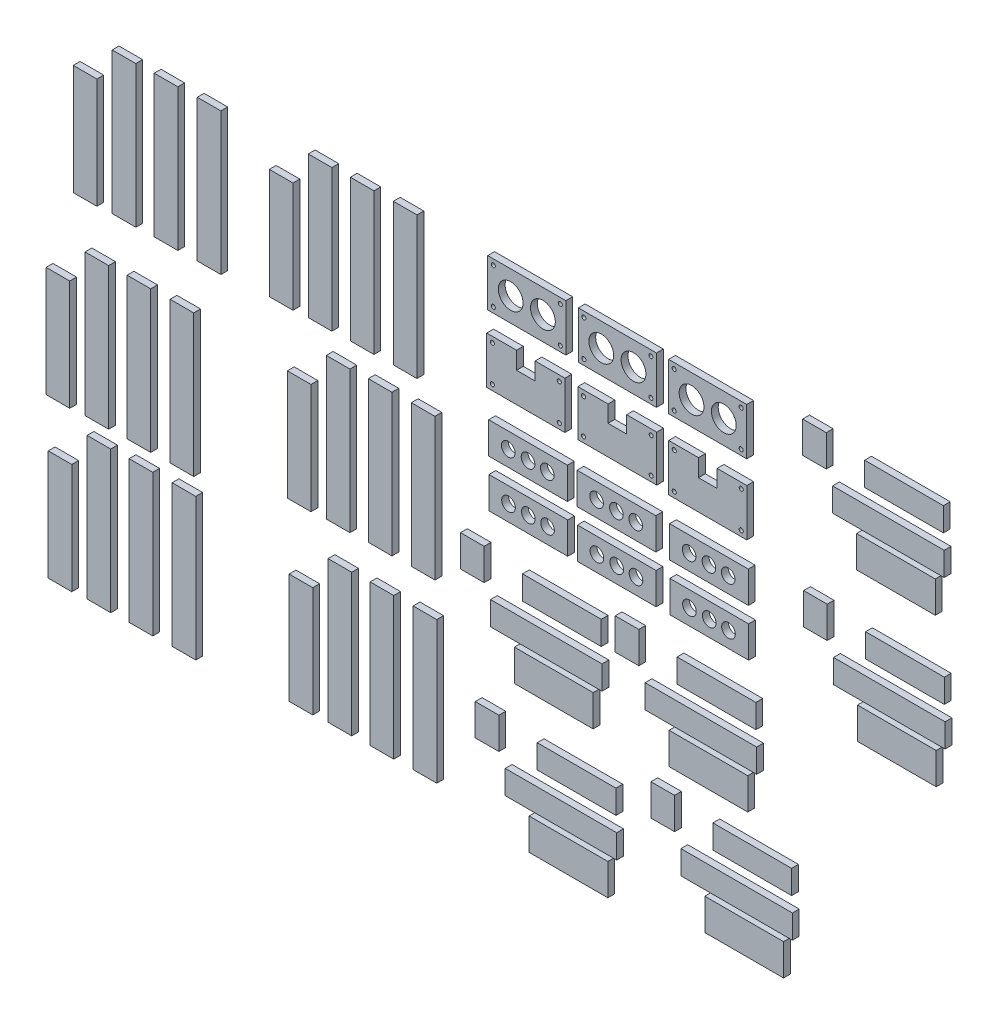
SolidWorks part; units mm, degrees
ref_plane "Alzado" through (0, 0, 0) normal (0, 0, 1) x (1, 0, 0)
ref_plane "Planta" through (0, 0, 0) normal (0, 1, 0) x (1, 0, 0)
ref_plane "Vista lateral" through (0, 0, 0) normal (1, 0, 0) x (0, 0, -1)
sketch "Croquis1" plane through (0, 0, 0) normal (0, 0, 1) x (1, 0, 0)
  line L0 (-40.6079, 0) -> (40.6079, 0) construction
  line L1 (-31.5, -19) -> (31.5, -19)
  line L2 (-31.5, -19) -> (-31.5, 19)
  line L3 (-31.5, 19) -> (31.5, 19)
  line L4 (31.5, -19) -> (31.5, 19)
  line L5 (-31.5, -19) -> (31.5, 19) construction
  line L6 (-31.5, 19) -> (31.5, -19) construction
  line L7 (0, 0) -> (0, -34.457) construction
  line L8 (-228.2882, -0.4654) -> (82.663, -0.4654) construction
  line L9 (-104.3126, -19.4654) -> (-41.3126, -19.4654)
  line L10 (-104.3126, -19.4654) -> (-104.3126, 18.5346)
  line L11 (-104.3126, 18.5346) -> (-41.3126, 18.5346)
  line L12 (-41.3126, -19.4654) -> (-41.3126, 18.5346)
  line L13 (-104.3126, -19.4654) -> (-41.3126, 18.5346) construction
  line L14 (-104.3126, 18.5346) -> (-41.3126, -19.4654) construction
  line L15 (-72.8126, -0.4654) -> (-72.8126, -34.9225) construction
  line L16 (-186.475, -0.4654) -> (-105.2592, -0.4654) construction
  line L17 (-177.3671, -19.4654) -> (-114.3671, -19.4654)
  line L18 (-177.3671, -19.4654) -> (-177.3671, 18.5346)
  line L19 (-177.3671, 18.5346) -> (-114.3671, 18.5346)
  line L20 (-114.3671, -19.4654) -> (-114.3671, 18.5346)
  line L21 (-177.3671, -19.4654) -> (-114.3671, 18.5346) construction
  line L22 (-177.3671, 18.5346) -> (-114.3671, -19.4654) construction
  line L23 (-145.8671, -0.4654) -> (-145.8671, -34.9225) construction
  line L24 (-146.6682, -54.9649) -> (-115.1682, -54.9649) construction
  line L25 (-178.1682, -73.9649) -> (-162.1682, -73.9649)
  line L26 (-178.1682, -73.9649) -> (-178.1682, -35.9649)
  line L27 (-178.1682, -35.9649) -> (-154.1682, -35.9649)
  line L28 (-115.1682, -73.9649) -> (-115.1682, -35.9649)
  line L29 (-178.1682, -73.9649) -> (-115.1682, -35.9649) construction
  line L30 (-178.1682, -35.9649) -> (-115.1682, -73.9649) construction
  line L31 (-146.6682, -54.9649) -> (-146.6682, -32.3728) construction
  line L32 (-131.1682, -73.9649) -> (-115.1682, -73.9649)
  line L33 (-139.1682, -35.9649) -> (-115.1682, -35.9649)
  line L34 (-154.1682, -35.9649) -> (-154.1682, -49.9649)
  line L35 (-154.1682, -49.9649) -> (-139.1682, -49.9649)
  line L36 (-139.1682, -35.9649) -> (-139.1682, -49.9649)
  line L37 (-162.1682, -73.9649) -> (-131.1682, -73.9649)
  line L38 (-72.8577, -55.1129) -> (-41.0716, -55.1129) construction
  line L39 (-104.6438, -73.6337) -> (-88.6438, -73.6337)
  line L40 (-104.6438, -73.6337) -> (-104.6438, -36.5921)
  line L41 (-104.6438, -36.5921) -> (-80.3577, -36.5921)
  line L42 (-41.0716, -73.6337) -> (-41.0716, -36.5921)
  line L43 (-104.6438, -73.6337) -> (-41.0716, -36.5921) construction
  line L44 (-104.6438, -36.5921) -> (-41.0716, -73.6337) construction
  line L45 (-72.8577, -55.1129) -> (-72.8577, -35.0223) construction
  line L46 (-57.6438, -73.6337) -> (-41.0716, -73.6337)
  line L47 (-65.3577, -36.5921) -> (-41.0716, -36.5921)
  line L48 (-80.3577, -36.5921) -> (-80.3577, -50.1129)
  line L49 (-80.3577, -50.1129) -> (-65.3577, -50.1129)
  line L50 (-65.3577, -36.5921) -> (-65.3577, -50.1129)
  line L51 (-88.6438, -73.6337) -> (-57.6438, -73.6337)
  line L52 (0.0494, -56.6209) -> (31.5494, -56.6209) construction
  line L53 (-31.4506, -75.6209) -> (-15.4506, -75.6209)
  line L54 (-31.4506, -75.6209) -> (-31.4506, -37.6209)
  line L55 (-31.4506, -37.6209) -> (-7.4506, -37.6209)
  line L56 (31.5494, -75.6209) -> (31.5494, -37.6209)
  line L57 (-31.4506, -75.6209) -> (31.5494, -37.6209) construction
  line L58 (-31.4506, -37.6209) -> (31.5494, -75.6209) construction
  line L59 (0.0494, -56.6209) -> (0.0494, -34.0287) construction
  line L60 (15.5494, -75.6209) -> (31.5494, -75.6209)
  line L61 (7.5494, -37.6209) -> (31.5494, -37.6209)
  line L62 (-7.4506, -37.6209) -> (-7.4506, -51.6209)
  line L63 (-7.4506, -51.6209) -> (7.5494, -51.6209)
  line L64 (7.5494, -37.6209) -> (7.5494, -51.6209)
  line L65 (-15.4506, -75.6209) -> (15.5494, -75.6209)
  line L66 (-288.1863, 17.873) -> (-269.1363, 17.873)
  line L67 (-253.4877, 18.4091) -> (-234.4377, 18.4091)
  line L68 (-253.4877, 18.4091) -> (-253.4877, -95.8909)
  line L69 (-253.4877, -95.8909) -> (-234.4377, -95.8909)
  line L70 (-234.4377, 18.4091) -> (-234.4377, -95.8909)
  line L71 (-288.1863, 17.873) -> (-288.1863, -96.427)
  line L72 (-288.1863, -96.427) -> (-269.1363, -96.427)
  line L73 (-269.1363, 17.873) -> (-269.1363, -96.427)
  line L74 (-322.0812, 17.1595) -> (-303.0312, 17.1595)
  line L75 (-322.0812, 17.1595) -> (-322.0812, -97.1405)
  line L76 (-322.0812, -97.1405) -> (-303.0312, -97.1405)
  line L77 (-303.0312, 17.1595) -> (-303.0312, -97.1405)
  line L78 (-353.4785, -9.3109) -> (-334.4285, -9.3109)
  line L79 (-353.4785, -9.3109) -> (-353.4785, -98.2109)
  line L80 (-353.4785, -98.2109) -> (-334.4285, -98.2109)
  line L81 (-334.4285, -9.3109) -> (-334.4285, -98.2109)
  line L82 (-50.4155, -216.2662) -> (39.5005, -216.2662)
  line L83 (-176.6177, -95.7144) -> (-113.1177, -95.7144)
  line L84 (-176.6177, -95.7144) -> (-176.6177, -121.1144)
  line L85 (-176.6177, -121.1144) -> (-113.1177, -121.1144)
  line L86 (-113.1177, -95.7144) -> (-113.1177, -121.1144)
  line L87 (-24.6254, -185.409) -> (38.8746, -185.409)
  line L88 (-24.6254, -185.409) -> (-24.6254, -204.459)
  line L89 (-24.6254, -204.459) -> (38.8746, -204.459)
  line L90 (38.8746, -185.409) -> (38.8746, -204.459)
  line L91 (-50.4155, -216.2662) -> (-50.4155, -235.3162)
  line L92 (-50.4155, -235.3162) -> (39.5005, -235.3162)
  line L93 (39.5005, -216.2662) -> (39.5005, -235.3162)
  line L94 (-105.3305, -95.344) -> (-41.8305, -95.344)
  line L95 (-105.3305, -95.344) -> (-105.3305, -120.744)
  line L96 (-31.1653, -239.8645) -> (32.3347, -239.8645)
  line L97 (-31.1653, -239.8645) -> (-31.1653, -265.2645)
  line L98 (-31.1653, -265.2645) -> (32.3347, -265.2645)
  line L99 (32.3347, -239.8645) -> (32.3347, -265.2645)
  line L100 (-74.5859, -181.6414) -> (-55.5359, -181.6414)
  line L101 (-74.5859, -181.6414) -> (-74.5859, -207.0414)
  line L102 (-74.5859, -207.0414) -> (-55.5359, -207.0414)
  line L103 (-55.5359, -181.6414) -> (-55.5359, -207.0414)
  line L104 (-105.3305, -120.744) -> (-41.8305, -120.744)
  line L105 (-41.8305, -95.344) -> (-41.8305, -120.744)
  line L106 (-30.7362, -95.344) -> (32.7638, -95.344)
  line L107 (-30.7362, -95.344) -> (-30.7362, -120.744)
  line L108 (-30.7362, -120.744) -> (32.7638, -120.744)
  line L109 (32.7638, -95.344) -> (32.7638, -120.744)
  line L110 (-176.3794, -133.8534) -> (-112.8794, -133.8534)
  line L111 (-176.3794, -133.8534) -> (-176.3794, -159.2534)
  line L112 (-176.3794, -159.2534) -> (-112.8794, -159.2534)
  line L113 (-112.8794, -133.8534) -> (-112.8794, -159.2534)
  line L114 (-105.0922, -133.4831) -> (-41.5922, -133.4831)
  line L115 (-105.0922, -133.4831) -> (-105.0922, -158.8831)
  line L116 (-105.0922, -158.8831) -> (-41.5922, -158.8831)
  line L117 (-41.5922, -133.4831) -> (-41.5922, -158.8831)
  line L118 (-30.4979, -133.4831) -> (33.0021, -133.4831)
  line L119 (-30.4979, -133.4831) -> (-30.4979, -158.8831)
  line L120 (-30.4979, -158.8831) -> (33.0021, -158.8831)
  line L121 (33.0021, -133.4831) -> (33.0021, -158.8831)
  line L122 (-446.3063, 11.4324) -> (-427.2563, 11.4324)
  line L123 (-411.6077, 11.9685) -> (-392.5577, 11.9685)
  line L124 (-411.6077, 11.9685) -> (-411.6077, -102.3315)
  line L125 (-411.6077, -102.3315) -> (-392.5577, -102.3315)
  line L126 (-392.5577, 11.9685) -> (-392.5577, -102.3315)
  line L127 (-446.3063, 11.4324) -> (-446.3063, -102.8676)
  line L128 (-446.3063, -102.8676) -> (-427.2563, -102.8676)
  line L129 (-427.2563, 11.4324) -> (-427.2563, -102.8676)
  line L130 (-480.2011, 10.7188) -> (-461.1511, 10.7188)
  line L131 (-480.2011, 10.7188) -> (-480.2011, -103.5812)
  line L132 (-480.2011, -103.5812) -> (-461.1511, -103.5812)
  line L133 (-461.1511, 10.7188) -> (-461.1511, -103.5812)
  line L134 (-511.5985, -15.7515) -> (-492.5485, -15.7515)
  line L135 (-511.5985, -15.7515) -> (-511.5985, -104.6515)
  line L136 (-511.5985, -104.6515) -> (-492.5485, -104.6515)
  line L137 (-492.5485, -15.7515) -> (-492.5485, -104.6515)
  line L138 (-468.2004, -140.5758) -> (-449.1504, -140.5758)
  line L139 (-433.5018, -140.0397) -> (-414.4518, -140.0397)
  line L140 (-433.5018, -140.0397) -> (-433.5018, -254.3397)
  line L141 (-433.5018, -254.3397) -> (-414.4518, -254.3397)
  line L142 (-414.4518, -140.0397) -> (-414.4518, -254.3397)
  line L143 (-468.2004, -140.5758) -> (-468.2004, -254.8758)
  line L144 (-468.2004, -254.8758) -> (-449.1504, -254.8758)
  line L145 (-449.1504, -140.5758) -> (-449.1504, -254.8758)
  line L146 (-502.0953, -141.2894) -> (-483.0453, -141.2894)
  line L147 (-502.0953, -141.2894) -> (-502.0953, -255.5894)
  line L148 (-502.0953, -255.5894) -> (-483.0453, -255.5894)
  line L149 (-483.0453, -141.2894) -> (-483.0453, -255.5894)
  line L150 (-533.4927, -167.7597) -> (-514.4427, -167.7597)
  line L151 (-533.4927, -167.7597) -> (-533.4927, -256.6597)
  line L152 (-533.4927, -256.6597) -> (-514.4427, -256.6597)
  line L153 (-514.4427, -167.7597) -> (-514.4427, -256.6597)
  line L154 (-273.655, -115.5539) -> (-254.605, -115.5539)
  line L155 (-238.9564, -115.0178) -> (-219.9064, -115.0178)
  line L156 (-238.9564, -115.0178) -> (-238.9564, -229.3178)
  line L157 (-238.9564, -229.3178) -> (-219.9064, -229.3178)
  line L158 (-219.9064, -115.0178) -> (-219.9064, -229.3178)
  line L159 (-273.655, -115.5539) -> (-273.655, -229.8539)
  line L160 (-273.655, -229.8539) -> (-254.605, -229.8539)
  line L161 (-254.605, -115.5539) -> (-254.605, -229.8539)
  line L162 (-307.5498, -116.2674) -> (-288.4998, -116.2674)
  line L163 (-307.5498, -116.2674) -> (-307.5498, -230.5674)
  line L164 (-307.5498, -230.5674) -> (-288.4998, -230.5674)
  line L165 (-288.4998, -116.2674) -> (-288.4998, -230.5674)
  line L166 (-338.9472, -142.7378) -> (-319.8972, -142.7378)
  line L167 (-338.9472, -142.7378) -> (-338.9472, -231.6378)
  line L168 (-338.9472, -231.6378) -> (-319.8972, -231.6378)
  line L169 (-319.8972, -142.7378) -> (-319.8972, -231.6378)
  line L170 (-466.5342, -267.8778) -> (-447.4842, -267.8778)
  line L171 (-431.8356, -267.3418) -> (-412.7856, -267.3418)
  line L172 (-431.8356, -267.3418) -> (-431.8356, -381.6418)
  line L173 (-431.8356, -381.6418) -> (-412.7856, -381.6418)
  line L174 (-412.7856, -267.3418) -> (-412.7856, -381.6418)
  line L175 (-466.5342, -267.8778) -> (-466.5342, -382.1778)
  line L176 (-466.5342, -382.1778) -> (-447.4842, -382.1778)
  line L177 (-447.4842, -267.8778) -> (-447.4842, -382.1778)
  line L178 (-500.429, -268.5914) -> (-481.379, -268.5914)
  line L179 (-500.429, -268.5914) -> (-500.429, -382.8914)
  line L180 (-500.429, -382.8914) -> (-481.379, -382.8914)
  line L181 (-481.379, -268.5914) -> (-481.379, -382.8914)
  line L182 (-531.8264, -295.0618) -> (-512.7764, -295.0618)
  line L183 (-531.8264, -295.0618) -> (-531.8264, -383.9618)
  line L184 (-531.8264, -383.9618) -> (-512.7764, -383.9618)
  line L185 (-512.7764, -295.0618) -> (-512.7764, -383.9618)
  line L186 (-272.2125, -256.7525) -> (-253.1625, -256.7525)
  line L187 (-237.5139, -256.2165) -> (-218.4639, -256.2165)
  line L188 (-237.5139, -256.2165) -> (-237.5139, -370.5165)
  line L189 (-237.5139, -370.5165) -> (-218.4639, -370.5165)
  line L190 (-218.4639, -256.2165) -> (-218.4639, -370.5165)
  line L191 (-272.2125, -256.7525) -> (-272.2125, -371.0525)
  line L192 (-272.2125, -371.0525) -> (-253.1625, -371.0525)
  line L193 (-253.1625, -256.7525) -> (-253.1625, -371.0525)
  line L194 (-306.1073, -257.4661) -> (-287.0573, -257.4661)
  line L195 (-306.1073, -257.4661) -> (-306.1073, -371.7661)
  line L196 (-306.1073, -371.7661) -> (-287.0573, -371.7661)
  line L197 (-287.0573, -257.4661) -> (-287.0573, -371.7661)
  line L198 (-337.5047, -283.9365) -> (-318.4547, -283.9365)
  line L199 (-337.5047, -283.9365) -> (-337.5047, -372.8365)
  line L200 (-337.5047, -372.8365) -> (-318.4547, -372.8365)
  line L201 (-318.4547, -283.9365) -> (-318.4547, -372.8365)
  line L202 (-175.1285, -220.5625) -> (-85.2125, -220.5625)
  line L203 (-149.3385, -189.7054) -> (-85.8385, -189.7054)
  line L204 (-149.3385, -189.7054) -> (-149.3385, -208.7554)
  line L205 (-149.3385, -208.7554) -> (-85.8385, -208.7554)
  line L206 (-85.8385, -189.7054) -> (-85.8385, -208.7554)
  line L207 (-175.1285, -220.5625) -> (-175.1285, -239.6125)
  line L208 (-175.1285, -239.6125) -> (-85.2125, -239.6125)
  line L209 (-85.2125, -220.5625) -> (-85.2125, -239.6125)
  line L210 (-155.8784, -244.1608) -> (-92.3784, -244.1608)
  line L211 (-155.8784, -244.1608) -> (-155.8784, -269.5608)
  line L212 (-155.8784, -269.5608) -> (-92.3784, -269.5608)
  line L213 (-92.3784, -244.1608) -> (-92.3784, -269.5608)
  line L214 (-199.299, -185.9377) -> (-180.249, -185.9377)
  line L215 (-199.299, -185.9377) -> (-199.299, -211.3377)
  line L216 (-199.299, -211.3377) -> (-180.249, -211.3377)
  line L217 (-180.249, -185.9377) -> (-180.249, -211.3377)
  line L218 (-163.2615, -332.5571) -> (-73.3455, -332.5571)
  line L219 (-137.4715, -301.6999) -> (-73.9715, -301.6999)
  line L220 (-137.4715, -301.6999) -> (-137.4715, -320.7499)
  line L221 (-137.4715, -320.7499) -> (-73.9715, -320.7499)
  line L222 (-73.9715, -301.6999) -> (-73.9715, -320.7499)
  line L223 (-163.2615, -332.5571) -> (-163.2615, -351.6071)
  line L224 (-163.2615, -351.6071) -> (-73.3455, -351.6071)
  line L225 (-73.3455, -332.5571) -> (-73.3455, -351.6071)
  line L226 (-144.0114, -356.1553) -> (-80.5114, -356.1553)
  line L227 (-144.0114, -356.1553) -> (-144.0114, -381.5553)
  line L228 (-144.0114, -381.5553) -> (-80.5114, -381.5553)
  line L229 (-80.5114, -356.1553) -> (-80.5114, -381.5553)
  line L230 (-187.432, -297.9322) -> (-168.382, -297.9322)
  line L231 (-187.432, -297.9322) -> (-187.432, -323.3322)
  line L232 (-187.432, -323.3322) -> (-168.382, -323.3322)
  line L233 (-168.382, -297.9322) -> (-168.382, -323.3322)
  line L234 (-21.5996, -317.7233) -> (68.3164, -317.7233)
  line L235 (4.1905, -286.8662) -> (67.6905, -286.8662)
  line L236 (4.1905, -286.8662) -> (4.1905, -305.9162)
  line L237 (4.1905, -305.9162) -> (67.6905, -305.9162)
  line L238 (67.6905, -286.8662) -> (67.6905, -305.9162)
  line L239 (-21.5996, -317.7233) -> (-21.5996, -336.7733)
  line L240 (-21.5996, -336.7733) -> (68.3164, -336.7733)
  line L241 (68.3164, -317.7233) -> (68.3164, -336.7733)
  line L242 (-2.3494, -341.3216) -> (61.1506, -341.3216)
  line L243 (-2.3494, -341.3216) -> (-2.3494, -366.7216)
  line L244 (-2.3494, -366.7216) -> (61.1506, -366.7216)
  line L245 (61.1506, -341.3216) -> (61.1506, -366.7216)
  line L246 (-45.77, -283.0985) -> (-26.72, -283.0985)
  line L247 (-45.77, -283.0985) -> (-45.77, -308.4985)
  line L248 (-45.77, -308.4985) -> (-26.72, -308.4985)
  line L249 (-26.72, -283.0985) -> (-26.72, -308.4985)
  line L250 (100.7786, -3.2485) -> (190.6946, -3.2485)
  line L251 (126.5687, 27.6086) -> (190.0687, 27.6086)
  line L252 (126.5687, 27.6086) -> (126.5687, 8.5586)
  line L253 (126.5687, 8.5586) -> (190.0687, 8.5586)
  line L254 (190.0687, 27.6086) -> (190.0687, 8.5586)
  line L255 (100.7786, -3.2485) -> (100.7786, -22.2985)
  line L256 (100.7786, -22.2985) -> (190.6946, -22.2985)
  line L257 (190.6946, -3.2485) -> (190.6946, -22.2985)
  line L258 (120.0287, -26.8468) -> (183.5287, -26.8468)
  line L259 (120.0287, -26.8468) -> (120.0287, -52.2468)
  line L260 (120.0287, -52.2468) -> (183.5287, -52.2468)
  line L261 (183.5287, -26.8468) -> (183.5287, -52.2468)
  line L262 (76.6081, 31.3763) -> (95.6581, 31.3763)
  line L263 (76.6081, 31.3763) -> (76.6081, 5.9763)
  line L264 (76.6081, 5.9763) -> (95.6581, 5.9763)
  line L265 (95.6581, 31.3763) -> (95.6581, 5.9763)
  line L266 (101.5203, -122.66) -> (191.4363, -122.66)
  line L267 (127.3103, -91.8028) -> (190.8103, -91.8028)
  line L268 (127.3103, -91.8028) -> (127.3103, -110.8528)
  line L269 (127.3103, -110.8528) -> (190.8103, -110.8528)
  line L270 (190.8103, -91.8028) -> (190.8103, -110.8528)
  line L271 (101.5203, -122.66) -> (101.5203, -141.71)
  line L272 (101.5203, -141.71) -> (191.4363, -141.71)
  line L273 (191.4363, -122.66) -> (191.4363, -141.71)
  line L274 (120.7704, -146.2582) -> (184.2704, -146.2582)
  line L275 (120.7704, -146.2582) -> (120.7704, -171.6582)
  line L276 (120.7704, -171.6582) -> (184.2704, -171.6582)
  line L277 (184.2704, -146.2582) -> (184.2704, -171.6582)
  line L278 (77.3498, -88.0352) -> (96.3998, -88.0352)
  line L279 (77.3498, -88.0352) -> (77.3498, -113.4352)
  line L280 (77.3498, -113.4352) -> (96.3998, -113.4352)
  line L281 (96.3998, -88.0352) -> (96.3998, -113.4352)
  circle A0 centre (27, 14.5) radius 1.65
  circle A2 centre (13, 0) radius 10
  circle A3 centre (-13, 0) radius 10
  circle A4 centre (27, -14.5) radius 1.65
  circle A5 centre (-27, -14.5) radius 1.65
  circle A6 centre (-27, 14.5) radius 1.65
  circle A7 centre (-45.8126, 14.0346) radius 1.65
  circle A8 centre (-59.8126, -0.4654) radius 10
  circle A9 centre (-85.8126, -0.4654) radius 10
  circle A10 centre (-45.8126, -14.9654) radius 1.65
  circle A11 centre (-99.8126, -14.9654) radius 1.65
  circle A12 centre (-99.8126, 14.0346) radius 1.65
  circle A13 centre (-118.8671, 14.0346) radius 1.65
  circle A14 centre (-132.8671, -0.4654) radius 10
  circle A15 centre (-158.8671, -0.4654) radius 10
  circle A16 centre (-118.8671, -14.9654) radius 1.65
  circle A17 centre (-172.8671, -14.9654) radius 1.65
  circle A18 centre (-172.8671, 14.0346) radius 1.65
  circle A19 centre (-119.6682, -40.4649) radius 1.65
  circle A20 centre (-173.6682, -40.4649) radius 1.65
  circle A21 centre (-173.6682, -69.4649) radius 1.65
  circle A22 centre (-119.6682, -69.4649) radius 1.65
  circle A23 centre (-45.5716, -41.0921) radius 1.65
  circle A24 centre (-100.1438, -41.0921) radius 1.65
  circle A25 centre (-100.1438, -69.1337) radius 1.65
  circle A26 centre (-45.5716, -69.1337) radius 1.65
  circle A27 centre (27.0494, -42.1209) radius 1.65
  circle A28 centre (-26.9506, -42.1209) radius 1.65
  circle A29 centre (-26.9506, -71.1209) radius 1.65
  circle A30 centre (27.0494, -71.1209) radius 1.65
  circle A31 centre (-160.8489, -108.4144) radius 5.5
  circle A32 centre (-144.8677, -108.4144) radius 5.5
  circle A33 centre (-129.3499, -108.4144) radius 5.5
  circle A34 centre (-89.5617, -108.044) radius 5.5
  circle A35 centre (-73.5805, -108.044) radius 5.5
  circle A36 centre (-58.0627, -108.044) radius 5.5
  circle A37 centre (-14.9674, -108.044) radius 5.5
  circle A38 centre (1.0138, -108.044) radius 5.5
  circle A39 centre (16.5316, -108.044) radius 5.5
  circle A40 centre (-160.6106, -146.5534) radius 5.5
  circle A41 centre (-144.6294, -146.5534) radius 5.5
  circle A42 centre (-129.1117, -146.5534) radius 5.5
  circle A43 centre (-89.3234, -146.1831) radius 5.5
  circle A44 centre (-73.3422, -146.1831) radius 5.5
  circle A45 centre (-57.8244, -146.1831) radius 5.5
  circle A46 centre (-14.7291, -146.1831) radius 5.5
  circle A47 centre (1.2521, -146.1831) radius 5.5
  circle A48 centre (16.7699, -146.1831) radius 5.5
  point P0 (0, 0)
  point P22 (-72.8126, -0.4654)
  point P23 (0, -19)
  point P44 (-72.8126, -19.4654)
  point P45 (-145.8671, -0.4654)
  point P66 (-145.8671, -19.4654)
  point P67 (-146.6682, -54.9649)
  point P89 (-146.6682, -49.9649)
  point P90 (-72.8577, -55.1129)
  point P112 (-72.8577, -50.1129)
  point P113 (0.0494, -56.6209)
  point P135 (0.0494, -51.6209)
  dimension "D2" = 20
  dimension "D5" = 3.3
  dimension "D9" = 20
  dimension "D12" = 3.3
  dimension "D17" = 20
  dimension "D20" = 3.3
  dimension "D24" = 3.3
  dimension "D29" = 3.3
  dimension "D34" = 3.3
  dimension "D40" = 63.5
  dimension "D45" = 11
  dimension "D1" = 26
  dimension "D3" = 13
  dimension "D4" = 63
  dimension "D6" = 4.5
  dimension "D7" = 4.5
  dimension "D8" = 26
  dimension "2" = 38
  dimension "D10" = 13
  dimension "D11" = 63
  dimension "D13" = 4.5
  dimension "D14" = 4.5
  dimension "D15" = 38
  dimension "D16" = 26
  dimension "D18" = 13
  dimension "D19" = 63
  dimension "D21" = 4.5
  dimension "D22" = 4.5
  dimension "D23" = 38
  dimension "D25" = 15
  dimension "D26" = 5
  dimension "D27" = 4.5
  dimension "D28" = 4.5
  dimension "D30" = 15
  dimension "D31" = 5
  dimension "D32" = 4.5
  dimension "D33" = 4.5
  dimension "D35" = 15
  dimension "D36" = 5
  dimension "D37" = 4.5
  dimension "D38" = 4.5
  dimension "D39" = 63.5
  dimension "D41" = 63.5
  dimension "D42" = 63.5
  dimension "D43" = 63.5
  dimension "D44" = 63.5
extrude "Saliente-Extruir1" add sketch "Croquis1" along normal blind 5.5
